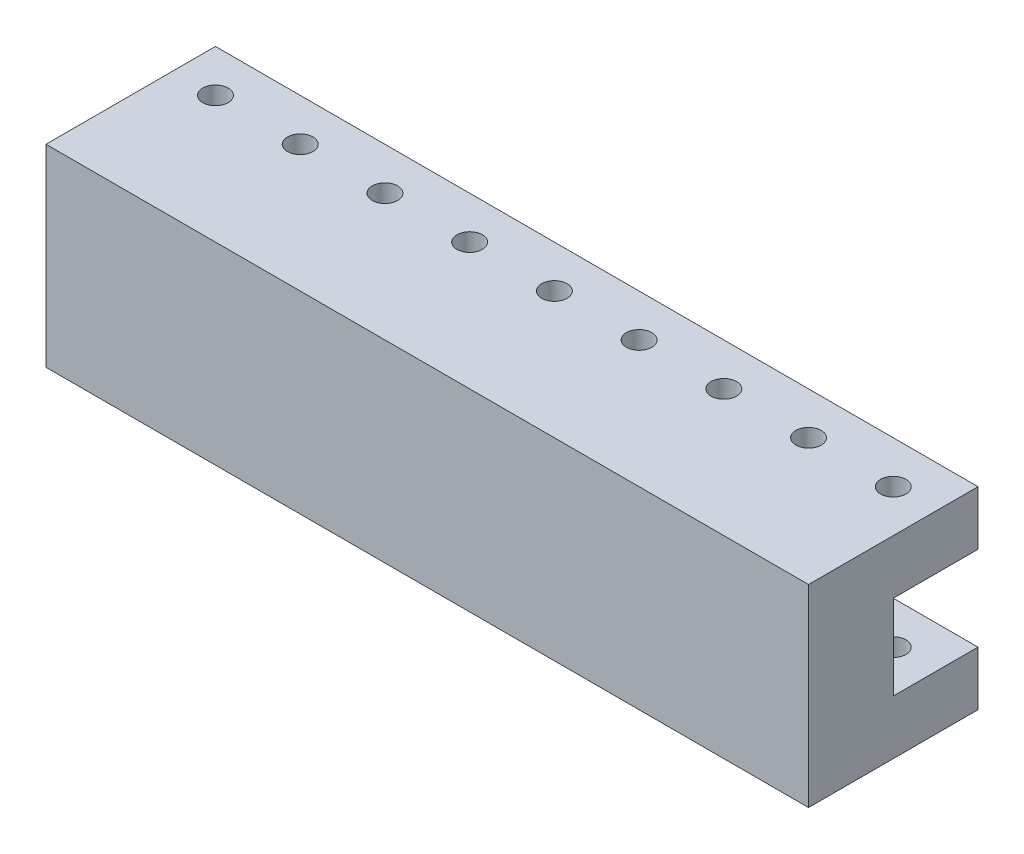
SolidWorks part; units mm, degrees
ref_plane "Front Plane" through (0, 0, 0) normal (0, 0, 1) x (1, 0, 0)
ref_plane "Top Plane" through (0, 0, 0) normal (0, 1, 0) x (1, 0, 0)
ref_plane "Right Plane" through (0, 0, 0) normal (1, 0, 0) x (0, 0, -1)
sketch "Sketch1" plane through (0, 0, 0) normal (0, 1, 0) x (1, 0, 0)
  line L1 (45, -5) -> (-45, -5)
  line L2 (45, -5) -> (45, 5)
  line L3 (45, 5) -> (-45, 5)
  line L4 (-45, -5) -> (-45, 5)
  line L5 (45, -5) -> (-45, 5) construction
  line L6 (45, 5) -> (-45, -5) construction
  point P0 (0, 0)
  dimension "D1" = 10
  dimension "D2" = 90
extrude "Boss-Extrude1" add sketch "Sketch1" along normal blind 22.8
sketch "Sketch2" plane through (0, 22.8, 0) normal (0, 1, 0) x (1, 0, 0)
  line L0 (-45, 5) -> (-45, -5) construction
  circle A0 centre (-40, 0) radius 1.5
  point P5 (0, 0)
  dimension "D2" = 3
  dimension "D1" = 5
extrude "Cut-Extrude1" cut sketch "Sketch2" against normal through all
pattern_linear "LPattern1" count 9 spacing 10 along (1, 0, 0) of "Cut-Extrude1"
sketch "Sketch3" plane through (45, 0, 0) normal (1, 0, 0) x (0, 0, -1)
  line L0 (-5, 22.8) -> (-5, 0) construction
  line L1 (-5, 6.4) -> (5, 6.4)
  line L2 (-5, 6.4) -> (-5, 16.4)
  line L3 (-5, 16.4) -> (5, 16.4)
  line L4 (5, 6.4) -> (5, 16.4)
  line L5 (5, 22.8) -> (5, 0) construction
  line L7 (-1007.234, 11.4) -> (48992.766, 11.4) construction
  point P8 (0, 0)
  dimension "D2" = 10
extrude "Cut-Extrude2" cut sketch "Sketch3" against normal through all
sketch "Sketch4" plane through (0, 0, 5) normal (0, 0, 1) x (1, 0, 0)
  line L1 (-45, 0) -> (45, 0)
  line L2 (-45, 0) -> (-45, 22.8)
  line L3 (-45, 22.8) -> (45, 22.8)
  line L4 (45, 0) -> (45, 22.8)
extrude "Boss-Extrude2" add sketch "Sketch4" along normal blind 10
